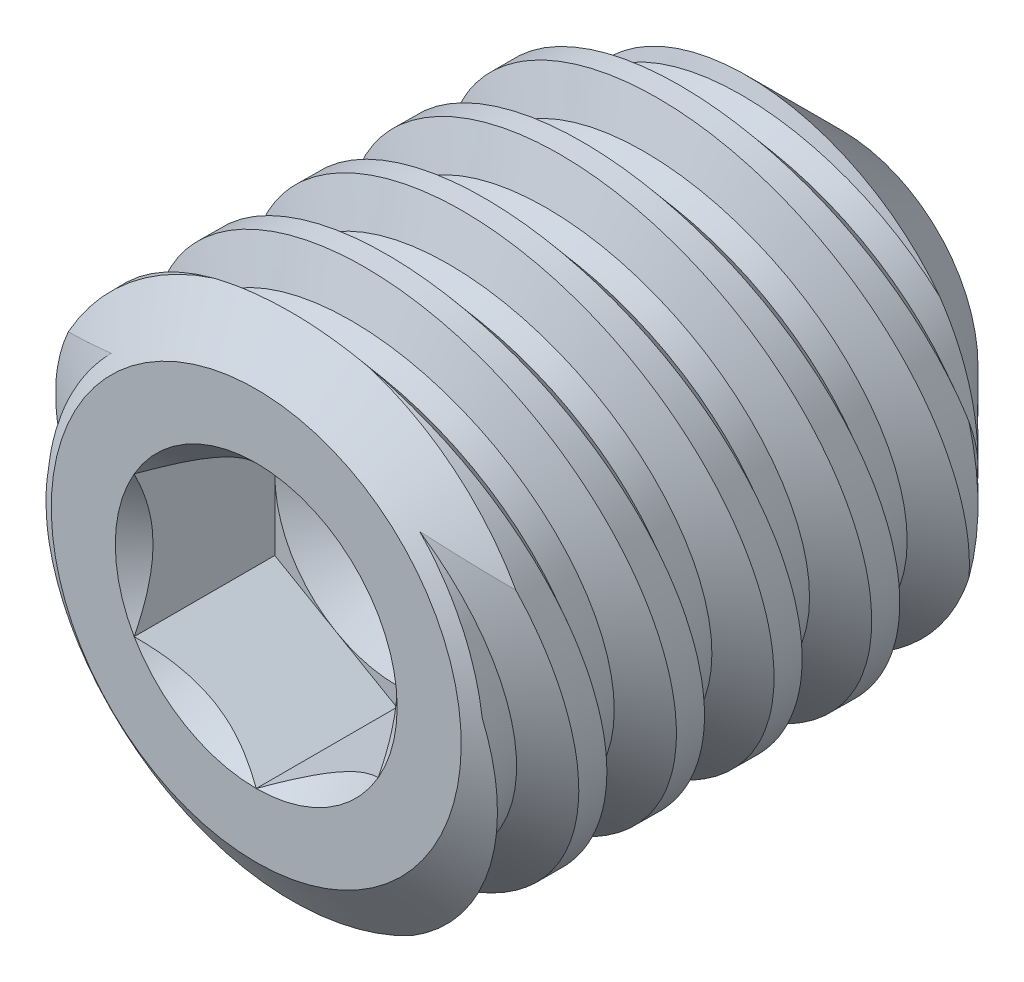
SolidWorks part; units mm, degrees
ref_plane "Front" through (0, 0, 0) normal (0, 0, 1) x (1, 0, 0)
ref_plane "Top" through (0, 0, 0) normal (0, 1, 0) x (1, 0, 0)
ref_plane "Right" through (0, 0, 0) normal (1, 0, 0) x (0, 0, -1)
sketch "Sketch22" plane through (0, 0, 0) normal (1, 0, 0) x (0, 0, -1)
  line L0 (-2.0493, 0) -> (-2.0493, 1.6662)
  line L1 (-2.0493, 1.6662) -> (-1.7576, 2.0828)
  line L2 (-1.7576, 2.0828) -> (1.7353, 2.0828)
  line L3 (1.7353, 2.0828) -> (2.7132, 1.1049)
  line L4 (2.7132, 1.1049) -> (2.0493, 0)
  line L5 (2.0493, 0) -> (-2.0493, 0)
  line L6 (2.0493, 0) -> (2.7132, 0) construction
  line L7 (2.7132, 0) -> (2.7132, 1.1049) construction
  line L8 (2.7132, -1.1049) -> (2.0493, 0) construction
  line L9 (-1.7576, -2.0828) -> (1.7353, -2.0828) construction
  dimension "Screw Dia" = 4.1656
  dimension "Length" = 4.7625
  dimension "D3" = 35
  dimension "Cup Point Dia" = 2.2098
  dimension "D5" = 118
  dimension "D6" = 45
  dimension "D7" = 3.3325
revolve "Revolve1" add sketch "Sketch22" angle 360 about L6
sketch "Sketch6" plane through (0, 0, 0) normal (1, 0, 0) x (0, 0, -1)
  line L0 (0.487, 2.0828) -> (1.2808, -2.0828) construction
  line L1 (-1.7576, 2.0828) -> (1.7353, 2.0828) construction
  line L2 (-1.7576, -2.0828) -> (1.7353, -2.0828) construction
  line L3 (0.487, 2.0828) -> (0.5845, 2.1014) construction
  line L4 (1.1035, 1.7629) -> (0.9086, 1.7258)
  line L5 (0.9086, 1.7258) -> (0.5845, 2.1014)
  line L6 (1.1035, 1.7629) -> (1.2667, 2.2314)
  line L7 (1.2667, 2.2314) -> (0.5845, 2.1014)
  line L8 (0.9415, 2.0828) -> (1.7353, -2.0828) construction
  line L9 (2.1898, 0.1622) -> (0.487, -0.1622) construction
  line L10 (0.9256, 2.1664) -> (1.006, 1.7443) construction
  line L13 (0.487, -2.0828) -> (0.487, 2.0828) construction
  line L14 (0.487, -2.0828) -> (1.2808, -2.0828) construction
  line L15 (1.2808, -2.0828) -> (1.7353, -2.0828) construction
  line L18 (0.487, 2.0828) -> (0.9415, 2.0828) construction
  point P18 (1.3384, 0)
  dimension "D1" = 0.7937
  dimension "D2" = 0.1984
  dimension "D3" = 60
  dimension "D4" = 0.0992
  dimension "Pitch" = 0.7937
revolve "Cut-Revolve8" cut sketch "Sketch6" angle 360 about L9
pattern_linear "LPattern1" count 5 spacing 0.7937 along (0, 0, 1) count 2 spacing 0.7937 along (0, 0, -1) of "Cut-Revolve8"
sketch "Sketch23" plane through (0, 0, 2.0493) normal (0, 0, 1) x (1, 0, 0)
  line L1 (0, 1.1457) -> (-0.9922, 0.5728)
  line L2 (-0.9922, 0.5728) -> (-0.9922, -0.5728)
  line L3 (-0.9922, -0.5728) -> (0, -1.1457)
  line L4 (0, -1.1457) -> (0.9922, -0.5728)
  line L5 (0.9922, -0.5728) -> (0.9922, 0.5728)
  line L6 (0.9922, 0.5728) -> (0, 1.1457)
  circle A0 centre (0, 0) radius 0.9922 construction
  dimension "Hex" = 1.9844
extrude "Cut-Extrude10" cut sketch "Sketch23" against normal blind 1.143
sketch "Sketch24" plane through (0, 0, 2.0493) normal (0, 0, 1) x (1, 0, 0)
  circle A0 centre (0, 0) radius 1.1457
extrude "Cut-Extrude11" cut sketch "Sketch24" against normal through all draft 45
sketch "Sketch26" plane through (0, 0, 0.9063) normal (0, 0, 1) x (1, 0, 0)
  circle A0 centre (0, 0) radius 0.9922 construction
  circle A1 centre (0, 0) radius 0.9922
extrude "Cut-Extrude12" cut sketch "Sketch26" against normal through all draft 59
equation "\"D2@Sketch6\"=\"Pitch@Sketch6\"/4"
equation "\"D4@Sketch6\"=\"Pitch@Sketch6\"/8"
equation "\"D1@Sketch6\"=\"Pitch@Sketch6\""
equation "\"D3@LPattern1\"=\"Pitch@Sketch6\""
equation "\"D1@LPattern1\"=(\"Length@Sketch22\"/\"Pitch@Sketch6\")-1"
equation "\"D4@LPattern1\"=\"Pitch@Sketch6\""
equation "\"D7@Sketch22\"=\"Screw Dia@Sketch22\"*.8"
